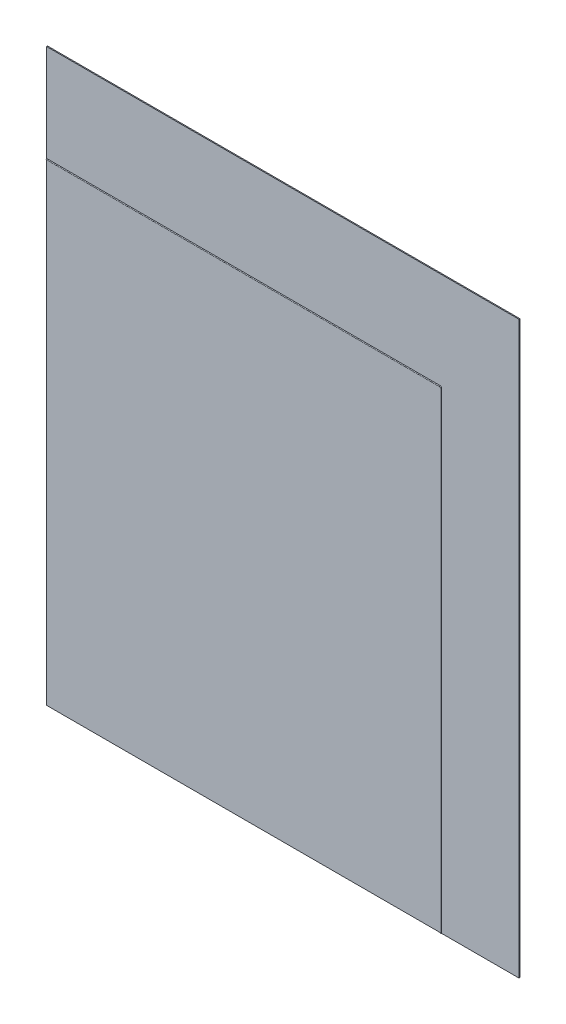
SolidWorks part; units mm, degrees
material "PE High Density"
ref_plane "Front Plane" through (0, 0, 0) normal (0, 0, 1) x (1, 0, 0)
ref_plane "Top Plane" through (0, 0, 0) normal (0, 1, 0) x (1, 0, 0)
ref_plane "Right Plane" through (0, 0, 0) normal (1, 0, 0) x (0, 0, -1)
sketch "Sketch1" plane through (0, 0, 0) normal (0, 0, 1) x (1, 0, 0)
  line L1 (-609.6, 736.6) -> (609.6, 736.6)
  line L2 (-609.6, 736.6) -> (-609.6, -736.6)
  line L3 (-609.6, -736.6) -> (609.6, -736.6)
  line L4 (609.6, 736.6) -> (609.6, -736.6)
  line L5 (-609.6, 736.6) -> (609.6, -736.6) construction
  line L6 (-609.6, -736.6) -> (609.6, 736.6) construction
  point P0 (0, 0)
  dimension "D1" = 1219.2
  dimension "D2" = 1473.2
extrude "Boss-Extrude1" add sketch "Sketch1" along normal blind 2.54
sketch "Sketch2" plane through (0, 0, 2.54) normal (0, 0, 1) x (1, 0, 0)
  line L0 (408.94, -736.6) -> (408.94, 482.6)
  line L1 (-609.6, -736.6) -> (609.6, -736.6) construction
  line L2 (406.4, 485.14) -> (-609.6, 485.14)
  line L3 (-609.6, 736.6) -> (-609.6, -736.6) construction
  arc A0 (408.94, 482.6) -> (406.4, 485.14) centre (406.4, 482.6) ccw
  point P7 (0, 0)
  dimension "D1" = 2.54
  dimension "D2" = 1016
  dimension "D3" = 1219.2
sweep "Sweep1" add path "Sketch2" circular profile diameter 2.54 parameters "D3"=2.54
